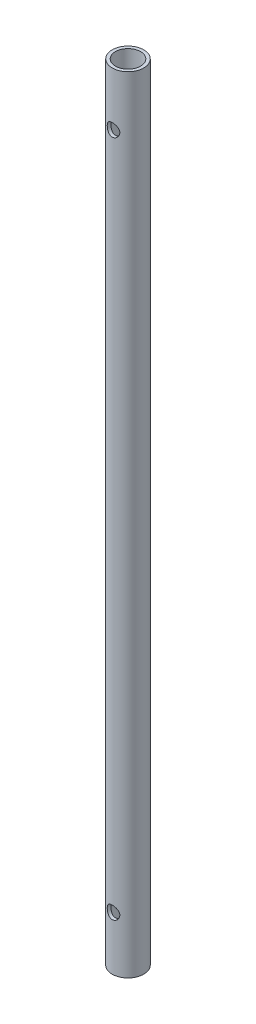
SolidWorks part; units mm, degrees
material "Thornel Mat VMA"
ref_plane "前视基准面" through (0, 0, 0) normal (0, 0, 1) x (1, 0, 0)
ref_plane "上视基准面" through (0, 0, 0) normal (0, 1, 0) x (1, 0, 0)
ref_plane "右视基准面" through (0, 0, 0) normal (1, 0, 0) x (0, 0, -1)
sketch "草图1" plane through (0, 0, 0) normal (0, 1, 0) x (1, 0, 0)
  circle A1 centre (0, 0) radius 5
  dimension "D1" = 10
extrude "拉伸-薄壁1" add sketch "草图1" along normal mid plane 249 thin thin type one direction reverse wall 1
sketch "草图2" plane through (0, 0, 0) normal (0, 0, 1) x (1, 0, 0)
  line L0 (-5, -124.5) -> (5, -124.5) construction
  line L1 (6.6, 0) -> (-6.6, 0) construction
  circle A0 centre (0, -107.5) radius 2
  circle A1 centre (0, 107.5) radius 2
  dimension "D1" = 4
  dimension "D2" = 17
extrude "切除-拉伸1" cut sketch "草图2" against normal through all both and the other way through all
